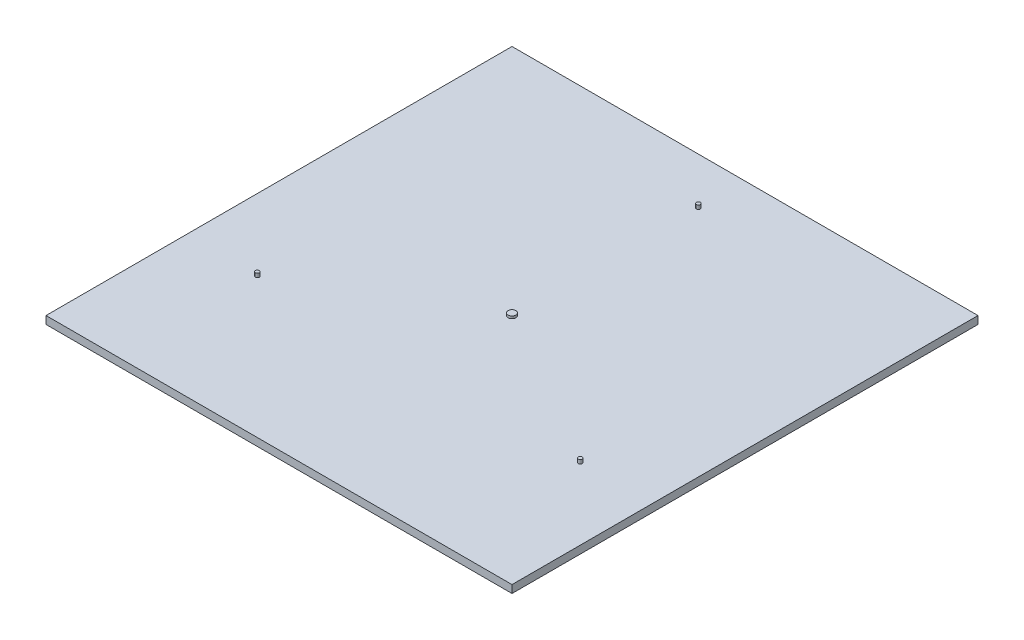
SolidWorks part; units mm, degrees
ref_plane "前视基准面" through (0, 0, 0) normal (0, 0, 1) x (1, 0, 0)
ref_plane "上视基准面" through (0, 0, 0) normal (0, 1, 0) x (1, 0, 0)
ref_plane "右视基准面" through (0, 0, 0) normal (1, 0, 0) x (0, 0, -1)
sketch "草图2" plane through (0, 0, 0) normal (0, 1, 0) x (1, 0, 0)
  line L0 (0, 0) -> (367.36, 0) construction
  line L1 (-300, 300) -> (300, 300)
  line L2 (-300, 300) -> (-300, -300)
  line L3 (-300, -300) -> (300, -300)
  line L4 (300, 300) -> (300, -300)
  line L5 (0, 0) -> (0, 203.84) construction
  dimension "D1" = 600
extrude "凸台-拉伸1" add sketch "草图2" along normal blind 10
sketch "草图3" plane through (0, 10, 0) normal (0, 1, 0) x (1, 0, 0)
  line L0 (0, 0) -> (0, 191.1668) construction
  line L1 (0, 0) -> (172.637, -99.672) construction
  line L2 (0, 0) -> (-151.1741, -87.2804) construction
  circle A0 centre (0, 240) radius 2.5
  circle A2 centre (-207.8461, -120) radius 2.5
  circle A3 centre (207.8461, -120) radius 2.5
  dimension "D3" = 5
  dimension "D1" = 120
  dimension "D2" = 120
  dimension "D4" = 240
  dimension "D5" = 240
  dimension "D6" = 240
extrude "凸台-拉伸2" add sketch "草图3" along normal blind 5
sketch "草图4" plane through (0, 10, 0) normal (0, 1, 0) x (1, 0, 0)
  circle A0 centre (0, 0) radius 5
  dimension "D1" = 10
extrude "凸台-拉伸3" add sketch "草图4" along normal blind 3
